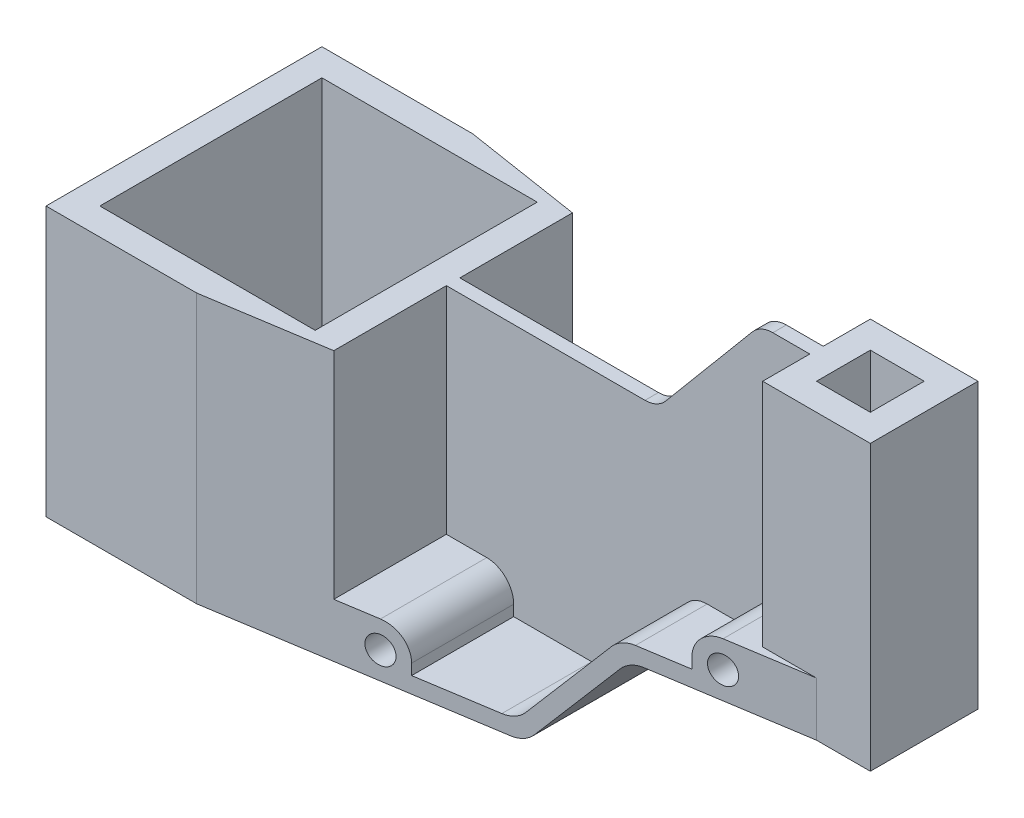
SolidWorks part; units mm, degrees
material "1060 Alloy"
ref_plane "Front Plane" through (0, 0, 0) normal (0, 0, 1) x (1, 0, 0)
ref_plane "Top Plane" through (0, 0, 0) normal (0, 1, 0) x (1, 0, 0)
ref_plane "Right Plane" through (0, 0, 0) normal (1, 0, 0) x (0, 0, -1)
sketch "Sketch1" plane through (0, 0, 0) normal (0, 0, 1) x (1, 0, 0)
  line L1 (-44.1979, 121.4031) -> (230.8021, 121.4031)
  line L2 (-44.1979, 121.4031) -> (-44.1979, -24.0969)
  line L3 (-44.1979, -24.0969) -> (230.8021, -24.0969)
  line L4 (230.8021, 121.4031) -> (230.8021, -24.0969)
extrude "Boss-Extrude1" add sketch "Sketch1" along normal blind 102.5
sketch "Sketch3" plane through (0, 0, 102.5) normal (0, 0, 1) x (1, 0, 0)
  line L5 (-44.1979, 121.4031) -> (70.8021, 121.4031)
  line L6 (-44.1979, 121.4031) -> (-44.1979, 75.9031)
  line L7 (-44.1979, 75.9031) -> (70.8021, 75.9031)
  line L8 (70.8021, 121.4031) -> (70.8021, 75.9031)
  line L9 (230.8021, -24.0969) -> (150.8021, -24.0969)
  line L10 (230.8021, -24.0969) -> (230.8021, 15.9031)
  line L11 (230.8021, 15.9031) -> (150.8021, 15.9031)
  line L12 (150.8021, -24.0969) -> (150.8021, 15.9031)
extrude "Cut-Extrude1" cut sketch "Sketch3" against normal blind 102.5
sketch "Sketch4" plane through (0, 75.9031, 0) normal (0, 1, 0) x (1, 0, 0)
  line L0 (-44.1979, -102.5) -> (70.8021, -102.5) construction
  line L1 (-44.1979, 0) -> (55.8021, 0)
  line L2 (-44.1979, 0) -> (-44.1979, -102.5)
  line L3 (-44.1979, -102.5) -> (55.8021, -102.5)
  line L4 (55.8021, 0) -> (55.8021, -102.5)
  line L5 (-34.1979, -10) -> (-34.1979, -92.5)
  line L6 (-34.1979, -92.5) -> (45.8021, -92.5)
  line L7 (45.8021, -10) -> (45.8021, -92.5)
  line L8 (-34.1979, -10) -> (45.8021, -10)
  dimension "D1" = 10
extrude "Cut-Extrude3" cut sketch "Sketch4" against normal blind 100 contours L5 L6 L7 L8
sketch "Sketch5" plane through (0, 0, 0) normal (0, 1, 0) x (1, 0, 0)
  line L1 (5.8021, 27.2897) -> (5.8021, -133.9135) construction
  line L2 (-66.589, -51.25) -> (262.1906, -51.25) construction
  line L3 (210.8021, 27.2897) -> (210.8021, -133.9135) construction
  line L4 (230.8021, -102.5) -> (230.8021, 0) construction
  line L5 (-44.1979, -102.5) -> (70.8021, -102.5) construction
  line L6 (-44.1979, 0) -> (55.8021, 0)
  line L7 (-44.1979, 0) -> (-44.1979, -102.5)
  line L8 (-44.1979, -102.5) -> (55.8021, -102.5)
  line L9 (55.8021, 0) -> (55.8021, -102.5)
  line L11 (-34.1979, -10) -> (-34.1979, -92.5) construction
  line L12 (45.8021, -10) -> (45.8021, -92.5) construction
  point P15 (5.8021, 0)
  dimension "D1" = 20
  dimension "D2" = 205
  dimension "D3" = 100
  dimension "D4" = 50
  dimension "D5" = 10
  dimension "D6" = 10
  dimension "D7" = 51.25
  dimension "D8" = 51.25
sketch "Sketch6" plane through (0, 121.4031, 0) normal (0, 1, 0) x (1, 0, 0)
  line L0 (230.8021, -102.5) -> (230.8021, 0) construction
  line L2 (230.8021, -51.25) -> (230.8021, -31.25)
  line L3 (230.8021, -31.25) -> (190.8035, -31.25)
  line L4 (190.8035, -51.25) -> (190.8035, -31.25)
  line L5 (200.8035, -51.25) -> (200.8035, -41.25)
  line L7 (190.8035, -51.25) -> (190.8035, -71.25)
  line L8 (190.8035, -71.25) -> (230.8021, -71.25)
  line L9 (230.8021, -51.25) -> (230.8021, -71.25)
  line L10 (220.8021, -41.25) -> (200.8035, -41.25)
  line L11 (220.8021, -51.25) -> (220.8021, -41.25)
  line L12 (220.8021, -51.25) -> (220.8021, -61.25)
  line L13 (200.8035, -61.25) -> (220.8021, -61.25)
  line L14 (200.8035, -51.25) -> (200.8035, -61.25)
  dimension "D1" = 10
extrude "Cut-Extrude4" cut sketch "Sketch6" against normal blind 105.5 contours L5 L10 L11 L12 L13 L14
sketch "Sketch7" plane through (0, 121.4031, 0) normal (0, 1, 0) x (1, 0, 0)
  line L5 (210.8021, 27.2897) -> (210.8021, -133.9135) construction
  line L11 (230.8021, 0) -> (210.8021, 0)
  line L12 (230.8021, 0) -> (230.8021, -31.25)
  line L13 (230.8021, -31.25) -> (210.8021, -31.25)
  line L14 (210.8021, 0) -> (210.8021, -31.25)
  line L15 (230.8021, -71.25) -> (210.8021, -71.25)
  line L16 (230.8021, -71.25) -> (230.8021, -102.8387)
  line L17 (230.8021, -102.8387) -> (210.8021, -102.8387)
  line L18 (210.8021, -71.25) -> (210.8021, -102.8387)
extrude "Cut-Extrude5" cut sketch "Sketch7" against normal blind 105.5
sketch "Sketch8" plane through (0, 121.4031, 0) normal (0, 1, 0) x (1, 0, 0)
  line L0 (190.8021, -31.25) -> (190.8021, -48.75)
  line L5 (190.8021, -48.75) -> (70.8021, -48.75)
  line L6 (70.8021, 0) -> (70.8021, -102.5) construction
  line L7 (70.8021, -48.75) -> (70.8021, 0)
  line L8 (70.8021, 0) -> (210.8021, 0)
  line L9 (210.8021, 0) -> (210.8021, -31.25)
  line L11 (190.8021, -71.25) -> (190.8021, -53.75)
  line L12 (190.8021, -53.75) -> (70.8021, -53.75)
  line L13 (70.8021, -53.75) -> (70.8021, -102.5)
  line L14 (70.8021, -102.5) -> (210.8021, -102.5)
  line L15 (210.8021, -102.5) -> (210.8021, -71.25)
  line L17 (210.8021, -31.25) -> (190.8021, -31.25)
  line L18 (190.8021, -71.25) -> (210.8021, -71.25)
extrude "Cut-Extrude7" cut sketch "Sketch8" against normal blind 85.5
sketch "Sketch10" plane through (0, 35.9031, 0) normal (0, 1, 0) x (1, 0, 0)
  line L1 (190.8021, -53.75) -> (70.8021, -53.75) construction
  line L2 (170.8021, -53.75) -> (170.8021, -102.5)
  line L3 (70.8021, -102.5) -> (210.8021, -102.5) construction
  line L4 (170.8021, -102.5) -> (70.8021, -102.5)
  line L5 (70.8021, -102.5) -> (70.8021, -53.75)
  line L6 (70.8021, -53.75) -> (170.8021, -53.75)
extrude "Cut-Extrude8" cut sketch "Sketch10" against normal blind 14
sketch "Sketch11" plane through (0, 35.9031, 0) normal (0, 1, 0) x (1, 0, 0)
  line L1 (70.8021, -48.75) -> (190.8021, -48.75) construction
  line L2 (170.8021, -48.75) -> (170.8021, 0)
  line L3 (210.8021, 0) -> (70.8021, 0) construction
  line L4 (170.8021, 0) -> (70.8021, 0)
  line L5 (70.8021, 0) -> (70.8021, -48.75)
  line L6 (70.8021, -48.75) -> (170.8021, -48.75)
extrude "Cut-Extrude9" cut sketch "Sketch11" against normal blind 14
sketch "Sketch12" plane through (0, 21.9031, 0) normal (0, 1, 0) x (1, 0, 0)
  line L0 (70.8021, -53.75) -> (80.8021, -53.75)
  line L1 (170.8021, -53.75) -> (70.8021, -53.75) construction
  line L2 (80.8021, -53.75) -> (80.8021, -102.5)
  line L3 (70.8021, -102.5) -> (170.8021, -102.5) construction
  line L4 (80.8021, -102.5) -> (70.8021, -102.5)
  line L5 (70.8021, -102.5) -> (70.8021, -53.75)
extrude "Cut-Extrude10" cut sketch "Sketch12" against normal blind 26
sketch "Sketch13" plane through (0, 21.9031, 0) normal (0, 1, 0) x (1, 0, 0)
  line L0 (170.8021, 0) -> (70.8021, 0) construction
  line L1 (70.8021, -48.75) -> (80.8021, -48.75)
  line L2 (70.8021, -48.75) -> (70.8021, 0)
  line L3 (70.8021, 0) -> (80.8021, 0)
  line L4 (80.8021, -48.75) -> (80.8021, 0)
extrude "Cut-Extrude12" cut sketch "Sketch13" against normal blind 26
sketch "Sketch14" plane through (0, 75.9031, 0) normal (0, 1, 0) x (1, 0, 0)
  line L1 (70.8021, -53.75) -> (55.8021, -53.75)
  line L2 (70.8021, -53.75) -> (70.8021, -102.5)
  line L3 (70.8021, -102.5) -> (55.8021, -102.5)
  line L4 (55.8021, -53.75) -> (55.8021, -102.5)
  line L5 (70.8021, -48.75) -> (55.8021, -48.75)
  line L6 (70.8021, -48.75) -> (70.8021, 0)
  line L7 (70.8021, 0) -> (55.8021, 0)
  line L8 (55.8021, -48.75) -> (55.8021, 0)
extrude "Cut-Extrude13" cut sketch "Sketch14" against normal blind 80
sketch "Sketch16" plane through (0, 0, 102.5) normal (0, 0, 1) x (1, 0, 0)
  line L0 (150.8021, 15.9031) -> (117.2381, -24.0969)
  line L3 (148.0042, 21.9031) -> (114.4403, -18.0969)
  line L4 (-44.1979, -24.0969) -> (150.8021, -24.0969) construction
  line L5 (80.8021, -4.0969) -> (80.8021, -18.0969)
  line L6 (80.8021, -18.0969) -> (114.4403, -18.0969)
  line L7 (210.8021, 15.9031) -> (150.8021, 15.9031) construction
  line L8 (150.8021, 15.9031) -> (150.8021, -24.0969)
  line L9 (150.8021, -24.0969) -> (117.2381, -24.0969)
  line L10 (148.0042, 21.9031) -> (80.8021, 21.9031)
  line L11 (80.8021, 21.9031) -> (80.8021, -4.0969)
  dimension "D1" = 6
  dimension "D2" = 6
  dimension "D3" = 6
  dimension "D4" = 130
extrude "Cut-Extrude14" cut sketch "Sketch16" against normal blind 102.5 contours L9 L0 L8
sketch "Sketch17" plane through (0, 0, 102.5) normal (0, 0, 1) x (1, 0, 0)
  line L0 (80.8021, -4.0969) -> (80.8021, -18.0969)
  line L1 (80.8021, -18.0969) -> (114.4403, -18.0969)
  line L2 (114.4403, -18.0969) -> (148.0042, 21.9031)
  line L3 (80.8021, 21.9031) -> (170.8021, 21.9031) construction
  line L4 (150.8021, 15.9031) -> (117.2381, -24.0969) construction
  line L5 (-44.1979, -24.0969) -> (117.2381, -24.0969) construction
  line L6 (148.0042, 21.9031) -> (80.8021, 21.9031)
  line L7 (80.8021, 21.9031) -> (80.8021, -4.0969)
  dimension "D1" = 6
  dimension "D2" = 6
  dimension "D3" = 130
extrude "Cut-Extrude15" cut sketch "Sketch17" against normal blind 48.75
sketch "Sketch18" plane through (0, 0, 0) normal (0, 0, -1) x (-1, 0, 0)
  line L0 (-80.8021, -4.0969) -> (-80.8021, -18.0969)
  line L1 (-80.8021, -18.0969) -> (-114.4403, -18.0969)
  line L2 (-114.4403, -18.0969) -> (-148.0042, 21.9031)
  line L3 (-80.8021, 21.9031) -> (-170.8021, 21.9031) construction
  line L4 (-150.8021, 15.9031) -> (-117.2381, -24.0969) construction
  line L5 (44.1979, -24.0969) -> (-117.2381, -24.0969) construction
  line L6 (-148.0042, 21.9031) -> (-80.8021, 21.9031)
  line L7 (-80.8021, 21.9031) -> (-80.8021, -4.0969)
  dimension "D1" = 6
  dimension "D2" = 6
  dimension "D3" = 130
extrude "Cut-Extrude16" cut sketch "Sketch18" against normal blind 48.75
sketch "Sketch19" plane through (0, 0, 53.75) normal (0, 0, 1) x (1, 0, 0)
  line L8 (70.8021, 75.9031) -> (134.2459, 75.9031)
  line L11 (70.8021, 121.4031) -> (70.8021, 75.9031)
  line L15 (134.2459, 75.9031) -> (172.425, 121.4031)
  line L16 (190.8021, 121.4031) -> (70.8021, 121.4031) construction
  line L17 (172.425, 121.4031) -> (70.8021, 121.4031)
  line L20 (114.4403, -18.0969) -> (148.0042, 21.9031) construction
  dimension "D1" = 45.25
extrude "Cut-Extrude17" cut sketch "Sketch19" against normal blind 5
sketch "Sketch23" plane through (0, -24.0969, 0) normal (0, -1, 0) x (1, 0, 0)
  line L1 (-44.1979, 102.5) -> (117.2381, 102.5) construction
  line L2 (11.8021, 102.5) -> (210.8021, 71.25)
  line L3 (210.8021, 71.25) -> (210.8021, 102.5)
  line L4 (210.8021, 102.5) -> (11.8021, 102.5)
extrude "Cut-Extrude18" cut sketch "Sketch23" against normal blind 105
sketch "Sketch24" plane through (0, 0, 0) normal (0, 0, -1) x (-1, 0, 0)
  circle A0 centre (-180.8021, 25.9031) radius 5
  circle A1 centre (-70.8021, -14.0969) radius 5
extrude "Cut-Extrude19" cut sketch "Sketch24" against normal blind 105
sketch "Sketch25" plane through (0, -24.0969, 0) normal (0, -1, 0) x (1, 0, 0)
  line L0 (11.8021, 0) -> (210.8021, 0)
  line L1 (-44.1979, 0) -> (117.2381, 0) construction
  line L2 (11.8021, 0) -> (210.8021, 31.25)
  line L3 (210.8021, 31.25) -> (210.8021, 0)
  line L4 (210.8021, 0) -> (150.8021, 0) construction
extrude "Cut-Extrude20" cut sketch "Sketch25" against normal blind 105
fillet "Fillet1" radius 10 1 edges at (80.8021, -4.0969, 72.7073)
fillet "Fillet2" radius 10 1 edges at (148.0042, 21.9031, 67.4307)
fillet "Fillet3" radius 10 1 edges at (170.8021, 35.9031, 65.6407)
fillet "Fillet4" radius 10 1 edges at (80.8021, -4.0969, 29.7927)
fillet "Fillet5" radius 10 1 edges at (148.0042, 21.9031, 35.0693)
fillet "Fillet6" radius 10 1 edges at (170.8021, 35.9031, 36.8593)
fillet "Fillet7" radius 10 1 edges at (114.4403, -18.0969, 32.4339)
fillet "Fillet8" radius 10 1 edges at (114.4403, -18.0969, 70.0661)
fillet "Fillet9" radius 10 1 edges at (134.2459, 75.9031, 51.25)
fillet "Fillet10" radius 10 1 edges at (172.425, 121.4031, 51.25)
fillet "Fillet11" radius 10 1 edges at (150.8021, 15.9031, 51.25)
fillet "Fillet12" radius 10 1 edges at (117.2381, -24.0969, 51.25)
sketch "Sketch27" plane through (0, 0, 0) normal (0, 1, 0) x (1, 0, 0)
  line L0 (-78.905, -51.25) -> (262.8801, -51.25) construction
  line L1 (5.8021, -142.3301) -> (5.8021, 46.9663) construction
  line L2 (210.8021, 46.9663) -> (210.8021, -142.3301) construction
  line L3 (-44.1979, 0) -> (-44.1979, -102.5) construction
  line L4 (55.8021, -6.9095) -> (55.8021, -48.75) construction
  line L5 (-44.1979, 0) -> (11.8021, 0) construction
  line L6 (-34.1979, -10) -> (45.8021, -10) construction
  line L7 (55.8021, -53.75) -> (55.8021, -95.5905) construction
  line L8 (45.8021, -10) -> (45.8021, -92.5) construction
  line L9 (-34.1979, -10) -> (-34.1979, -92.5) construction
  line L10 (109.7772, -48.75) -> (80.8021, -48.75) construction
  line L11 (80.8021, -53.75) -> (109.7772, -53.75) construction
  line L12 (230.8021, -71.25) -> (230.8021, -31.25) construction
  line L13 (190.8021, -71.25) -> (190.8021, -53.75) construction
  point P26 (95.2896, -53.75)
  dimension "D1" = 50
  dimension "D2" = 100
  dimension "D3" = 51.25
  dimension "D4" = 10
  dimension "D5" = 10
  dimension "D6" = 10
  dimension "D7" = 6
  dimension "D8" = 2.5
  dimension "D9" = 5
  dimension "D10" = 205
  dimension "D11" = 20
  dimension "D12" = 40
sketch "Sketch28" plane through (0, 0, 0) normal (0, 0, 1) x (1, 0, 0)
  line L0 (-44.1979, 75.9031) -> (-44.1979, -24.0969)
  line L1 (-44.1979, -24.0969) -> (80.8021, -24.0969)
  line L2 (11.8021, -24.0969) -> (112.575, -24.0969) construction
  line L3 (-44.1979, 75.9031) -> (55.8021, 75.9031)
  line L4 (80.8021, -18.0969) -> (109.7772, -18.0969) construction
  line L5 (117.4376, -14.5248) -> (145.0069, 18.3309) construction
  line L6 (147.8047, 12.3309) -> (120.2355, -20.5248) construction
  line L7 (137.2433, 79.4752) -> (169.4276, 117.8309) construction
  line L8 (210.8021, 35.9031) -> (190.8021, 35.9031) construction
  line L9 (210.8021, 15.9031) -> (155.4652, 15.9031) construction
  line L10 (190.8021, 35.9031) -> (190.8021, 121.4031) construction
  line L11 (230.8021, 15.9031) -> (230.8021, 121.4031) construction
  line L12 (80.8021, -14.0969) -> (80.8021, -18.0969) construction
  line L13 (55.8021, -4.0969) -> (70.8021, -4.0969) construction
  dimension "D1" = 100
  dimension "D2" = 100
  dimension "D3" = 115
  dimension "D4" = 6
  dimension "D5" = 6
  dimension "D6" = 51.25
  dimension "D7" = 20
  dimension "D8" = 40
  dimension "D9" = 10
  dimension "D10" = 10
  dimension "D11" = 20
  dimension "D12" = 130
